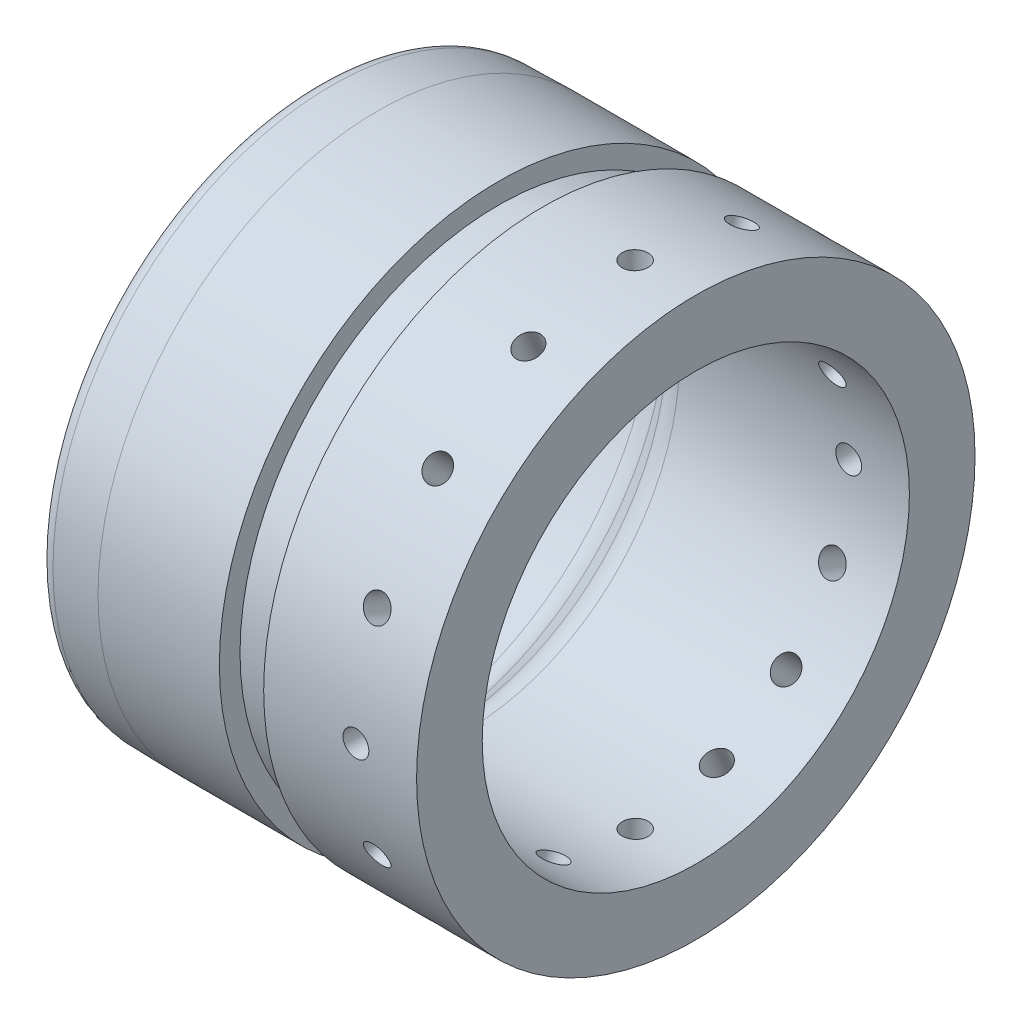
SolidWorks part; units mm, degrees
material "6061-T6 (SS)"
ref_plane "Front Plane" through (0, 0, 0) normal (0, 0, 1) x (1, 0, 0)
ref_plane "Top Plane" through (0, 0, 0) normal (0, 1, 0) x (1, 0, 0)
ref_plane "Right Plane" through (0, 0, 0) normal (1, 0, 0) x (0, 0, -1)
sketch "Sketch1" plane through (0, 0, 0) normal (0, 0, 1) x (1, 0, 0)
  line L12 (0.0186, 58.9466) -> (98.3939, 58.9466) construction
  line L19 (-3.9714, 6.5774) -> (1.8338, 12.3827)
  line L28 (6.324, 14.2426) -> (54.4937, 14.2426)
  line L29 (54.4937, 0.5012) -> (54.4937, 14.2426)
  line L30 (13.2187, 0.5012) -> (13.2187, 4.8192)
  line L31 (13.2187, 4.8192) -> (22.4897, 4.8192)
  line L32 (22.4897, 4.8192) -> (22.4897, 0.5012)
  line L33 (22.4897, 0.5012) -> (54.4937, 0.5012)
  line L34 (-24.8999, 0.5012) -> (13.2187, 0.5012)
  line L35 (-24.8999, 0.5012) -> (-12.1813, 0.5012)
  line L36 (-12.1813, 0.5012) -> (-24.8999, 0.7232)
  line L38 (-24.8999, 4.7176) -> (-8.4616, 4.7176)
  line L39 (-24.8999, 4.7176) -> (-24.8999, 0.7232)
  line L40 (-24.8999, 0.7232) -> (-24.8999, 0.5012)
  arc A0 (-3.9714, 6.5774) -> (-8.4616, 4.7176) centre (-8.4616, 11.0676) cw
  arc A1 (6.324, 14.2426) -> (1.8338, 12.3827) centre (6.324, 7.8926) ccw
  point P8 (-5.8499, 4.2164)
  point P22 (3.6751, 13.7414)
  dimension "D15" = 4.7176
  dimension "D16" = 4.8192
  dimension "D8" = 3.9714
  dimension "D9" = 5.8499
  dimension "D1" = 6.35
  dimension "D3" = 3.6751
  dimension "D2" = 1.8338
  dimension "D4" = 6.324
  dimension "D5" = 13.2187
  dimension "D6" = 22.4897
  dimension "D7" = 54.4937
  dimension "D10" = 0.5012
  dimension "D11" = 12.1813
  dimension "D12" = 24.8999
  dimension "D13" = 0.7232
  dimension "D14" = 4.2164
  dimension "D21" = 13.7414
  dimension "D23" = 58.9466
revolve "Revolve1" add sketch "Sketch1" angle 360 about L12
ref_plane "Tap Reference Plane" through (0, 0, -58.4454) normal (0, 0, -1) x (-1, 0, 0)
sketch "Tap Reference" plane through (0, 0, -58.4454) normal (0, 0, -1) x (-1, 0, 0)
  line L0 (-54.4937, 58.9466) -> (-41.7937, 58.9466)
  line L2 (-54.4937, 117.392) -> (-54.4937, 0.5012) construction
  point P5 (-41.7937, 58.9466)
hole_wizard "Tap Drill for 1/4-28 Tap1" positions "Sketch4" profile "Sketch6" hole size "1/4-28" standard "ANSI Inch" end condition through all
sketch "Sketch4" plane through (0, 0, -58.4454) normal (0, 0, -1) x (-1, 0, 0)
  point P0 (-41.7937, 58.9466)
sketch "Sketch6" plane through (41.7937, 58.9466, -58.4454) normal (1, 0, 0) x (0, 1, 0)
  line L0 (0, 0) -> (0, 116.8908)
  line L1 (0, 116.8908) -> (2.7051, 116.8908)
  line L2 (2.7051, 116.8908) -> (2.7051, 0)
  line L5 (2.7051, 0) -> (0, 0)
  line L11 (0, -6.35) -> (0, 107.95) construction
  dimension "Thru Hole Dia." = 5.4102
  dimension "Thru Hole Depth" = 116.8908
pattern_circular "Tap Pattern" count 16 over 360 about axis through (0.0186, 58.9466, 0) along (1, 0, 0) of "Tap Drill for 1/4-28 Tap1"
fillet "Fillet1" radius 3.175 1 edges at (-24.8999, 58.9466, 58.2234)
ref_plane "Plane1" through (54.4937, 0, 0) normal (1, 0, 0) x (0, 0, -1)
ref_plane "Plane2" through (-24.8999, 0, 0) normal (-1, 0, 0) x (0, 0, 1)
